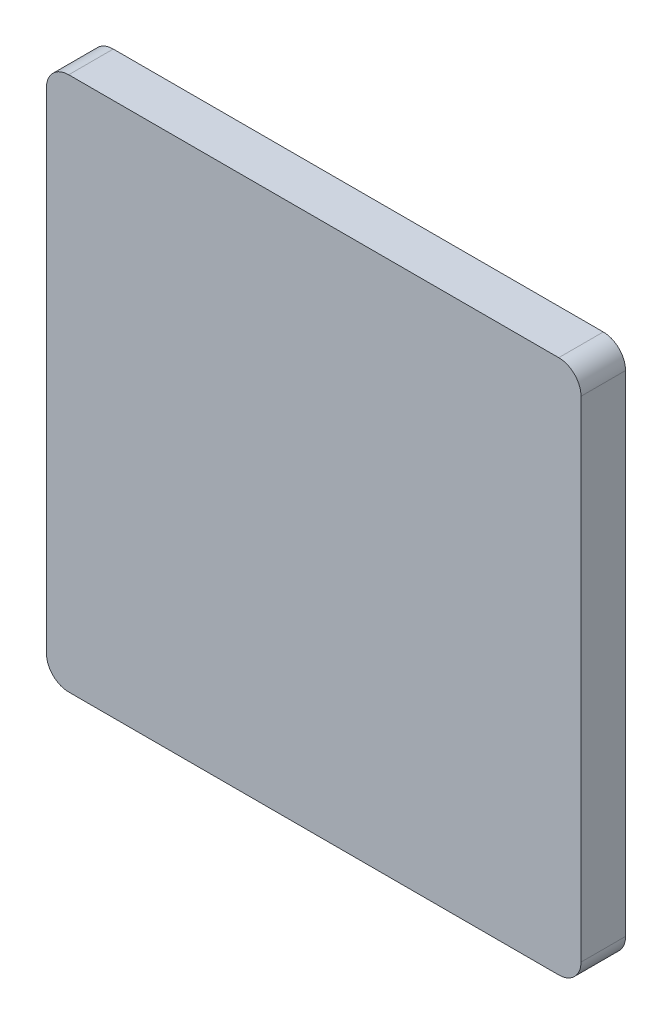
SolidWorks part; units mm, degrees
ref_plane "Front Plane" through (0, 0, 0) normal (0, 0, 1) x (1, 0, 0)
ref_plane "Top Plane" through (0, 0, 0) normal (0, 1, 0) x (1, 0, 0)
ref_plane "Right Plane" through (0, 0, 0) normal (1, 0, 0) x (0, 0, -1)
sketch "Sketch1" plane through (0, 0, 0) normal (0, 0, 1) x (1, 0, 0)
  line L1 (-38.1, 38.1) -> (38.1, 38.1)
  line L2 (-38.1, 38.1) -> (-38.1, -38.1)
  line L3 (-38.1, -38.1) -> (38.1, -38.1)
  line L4 (38.1, 38.1) -> (38.1, -38.1)
  line L5 (-38.1, 38.1) -> (38.1, -38.1) construction
  line L6 (-38.1, -38.1) -> (38.1, 38.1) construction
  point P0 (0, 0)
  dimension "D1" = 76.2
  dimension "D2" = 76.2
extrude "Boss-Extrude1" add sketch "Sketch1" along normal mid plane 6.35
fillet "Fillet1" radius 3.175 4 edges at (-38.1, 38.1, 0) (-38.1, -38.1, 0) (38.1, -38.1, 0) (38.1, 38.1, 0)
sketch "Sketch2" plane through (0, 0, 3.175) normal (0, 0, 1) x (1, 0, 0)
  line L0 (0, 38.1) -> (0, -38.1) construction
  line L1 (34.925, 38.1) -> (-34.925, 38.1) construction
  line L2 (-34.925, -38.1) -> (34.925, -38.1) construction
  line L3 (-38.1, 0) -> (38.1, 0) construction
  line L4 (-38.1, 34.925) -> (-38.1, -34.925) construction
  line L5 (38.1, -34.925) -> (38.1, 34.925) construction
